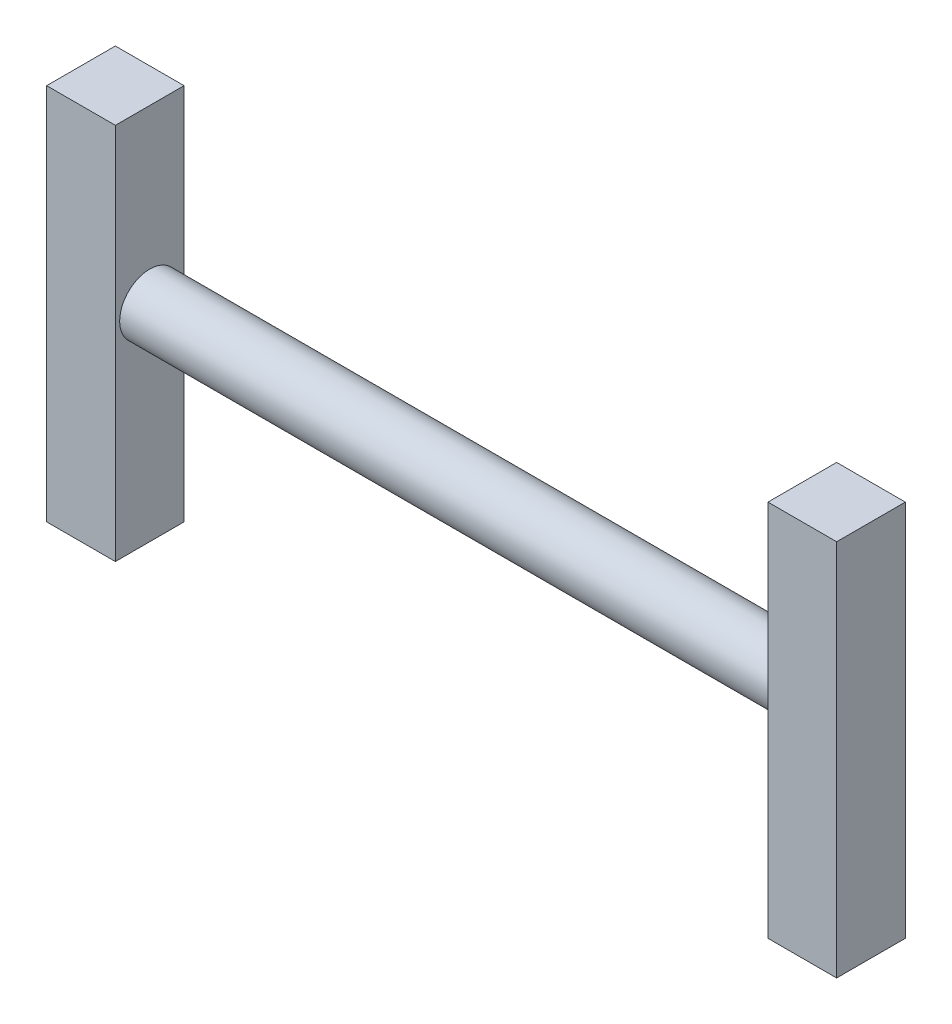
SolidWorks part; units mm, degrees
ref_plane "Front Plane" through (0, 0, 0) normal (0, 0, 1) x (1, 0, 0)
ref_plane "Top Plane" through (0, 0, 0) normal (0, 1, 0) x (1, 0, 0)
ref_plane "Right Plane" through (0, 0, 0) normal (1, 0, 0) x (0, 0, -1)
sketch "Sketch1" plane through (0, 0, 0) normal (0, 1, 0) x (1, 0, 0)
  line L1 (-20, -20) -> (20, -20)
  line L2 (-20, -20) -> (-20, 20)
  line L3 (-20, 20) -> (20, 20)
  line L4 (20, -20) -> (20, 20)
  line L5 (-20, -20) -> (20, 20) construction
  line L6 (-20, 20) -> (20, -20) construction
  point P0 (0, 0)
  dimension "D1" = 40
extrude "Boss-Extrude1" add sketch "Sketch1" along normal mid plane 220
sketch "Sketch2" plane through (0, 0, 0) normal (1, 0, 0) x (0, 0, -1)
  line L0 (0, 110) -> (0, -110) construction
  line L1 (-20, 110) -> (20, 110) construction
  line L2 (-20, -110) -> (20, -110) construction
  circle A0 centre (0, 10) radius 17.5
  point P6 (0, 10)
  dimension "D2" = 35
  dimension "D1" = 100
extrude "Boss-Extrude2" add sketch "Sketch2" along normal blind 210
ref_plane "Plane1" through (210, 0, 0) normal (1, 0, 0) x (0, 0, -1)
mirror "Mirror7" about plane through (210, 10, 0) normal (1, 0, 0) of bodies 102
